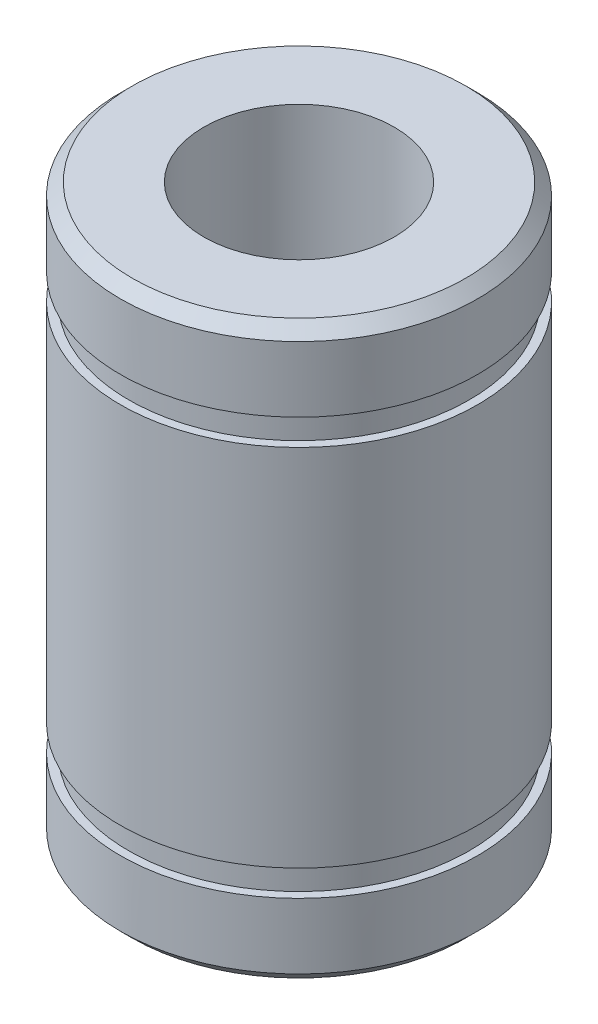
SolidWorks part; units mm, degrees
ref_plane "Front Plane" through (0, 0, 0) normal (0, 0, 1) x (1, 0, 0)
ref_plane "Top Plane" through (0, 0, 0) normal (0, 1, 0) x (1, 0, 0)
ref_plane "Right Plane" through (0, 0, 0) normal (1, 0, 0) x (0, 0, -1)
sketch "Sketch1" plane through (0, 0, 0) normal (0, 0, 1) x (1, 0, 0)
  line L0 (4, 0) -> (4, 12)
  line L1 (4, 12) -> (7.5, 12)
  line L2 (7.5, 12) -> (7.5, 8.75)
  line L3 (7.5, 8.75) -> (7.15, 8.75)
  line L4 (7.15, 8.75) -> (7.15, 7.65)
  line L5 (7.15, 7.65) -> (7.5, 7.65)
  line L6 (7.5, 7.65) -> (7.5, 0)
  line L7 (7.5, 0) -> (4, 0)
  line L8 (0, 0) -> (0, 12) construction
  line L9 (0, 0) -> (7.5, 0) construction
  point P11 (0, 48.4898)
  point P12 (7.325, 8.75)
  dimension "D1" = 1.1
  dimension "D2" = 24
  dimension "D3" = 17.5
  dimension "D4" = 8
  dimension "D5" = 15
  dimension "D6" = 14.3
revolve "Revolve1" add sketch "Sketch1" angle 360 about L8
chamfer "Chamfer1" distance 0.5 angle 45 1 edges at (0, 12, -7.5)
mirror "Mirror1" about plane through (7.5, 0, 0) normal (0, -1, 0) of bodies 101
